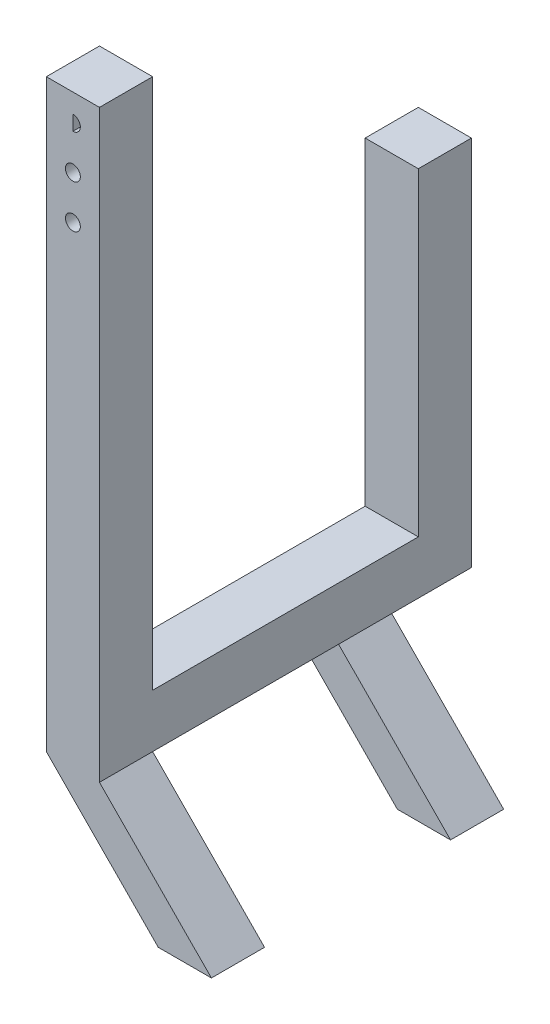
SolidWorks part; units mm, degrees
ref_plane "Front Plane" through (0, 0, 0) normal (0, 0, 1) x (1, 0, 0)
ref_plane "Top Plane" through (0, 0, 0) normal (0, 1, 0) x (1, 0, 0)
ref_plane "Right Plane" through (0, 0, 0) normal (1, 0, 0) x (0, 0, -1)
sketch "Sketch1" plane through (0, 0, 0) normal (0, 0, 1) x (1, 0, 0)
  line L1 (0, 0) -> (12.7, 0)
  line L2 (0, 0) -> (0, 139.7)
  line L3 (0, 139.7) -> (12.7, 139.7)
  line L4 (12.7, 0) -> (12.7, 139.7)
  dimension "D1" = 12.7
  dimension "D2" = 139.7
extrude "Boss-Extrude1" add sketch "Sketch1" along normal blind 12.7 contours L2 L1 L4 L3
sketch "Sketch2" plane through (0, 0, 0) normal (-1, 0, 0) x (0, 0, 1)
  line L1 (0, 0) -> (-63.5, 0)
  line L2 (0, 0) -> (0, 12.7)
  line L3 (0, 12.7) -> (-63.5, 12.7)
  line L4 (-63.5, 0) -> (-63.5, 12.7)
  dimension "D1" = 63.5
  dimension "D2" = 12.7
extrude "Boss-Extrude2" add sketch "Sketch2" against normal blind 12.7 contours L2 L1 L4 L3
sketch "Sketch3" plane through (0, 0, 0) normal (-1, 0, 0) x (0, 0, 1)
  line L1 (-63.5, 0) -> (-76.2, 0)
  line L2 (-63.5, 0) -> (-63.5, 88.9)
  line L3 (-63.5, 88.9) -> (-76.2, 88.9)
  line L4 (-76.2, 0) -> (-76.2, 88.9)
  dimension "D1" = 12.7
  dimension "D2" = 88.9
extrude "Boss-Extrude3" add sketch "Sketch3" against normal blind 12.7
sketch "Sketch4" plane through (0, 0, 12.7) normal (0, 0, 1) x (1, 0, 0)
  line L0 (12.7, 0) -> (39.4531, -27.1272)
  line L1 (39.4531, -27.1272) -> (26.7531, -27.1272)
  line L2 (26.7531, -27.1272) -> (0, 0)
  line L3 (0, 0) -> (12.7, 0)
  dimension "D1" = 38.1
  dimension "D2" = 38.1
  dimension "D3" = 12.7
extrude "Boss-Extrude5" add sketch "Sketch4" against normal blind 12.7
sketch "Sketch5" plane through (0, 0, -76.2) normal (0, 0, -1) x (-1, 0, 0)
  line L0 (0, 0) -> (-26.7531, -27.1272)
  line L1 (-26.7531, -27.1272) -> (-39.4531, -27.1272)
  line L2 (-39.4531, -27.1272) -> (-12.7, 0)
  line L3 (-12.7, 0) -> (0, 0)
extrude "Boss-Extrude6" add sketch "Sketch5" against normal blind 12.7 from offset 19.05 offset against normal yes
sketch "Sketch6" plane through (0, 0, 12.7) normal (0, 0, 1) x (1, 0, 0)
  line L0 (6.35, 139.7) -> (6.35, 133.35)
  line L1 (0, 139.7) -> (12.7, 139.7) construction
  line L2 (6.35, 139.7) -> (6.35, 112.7125)
  line L3 (6.35, 133.35) -> (6.35, 112.7125)
  circle A0 centre (6.35, 133.35) radius 1.778
  circle A1 centre (6.35, 112.7125) radius 1.778
  circle A2 centre (6.35, 123.0312) radius 1.778
  dimension "D2" = 3.556
  dimension "D4" = 3.556
  dimension "D5" = 3.556
  dimension "D1" = 6.35
  dimension "D3" = 26.9875
extrude "Cut-Extrude1" cut sketch "Sketch6" against normal through all
